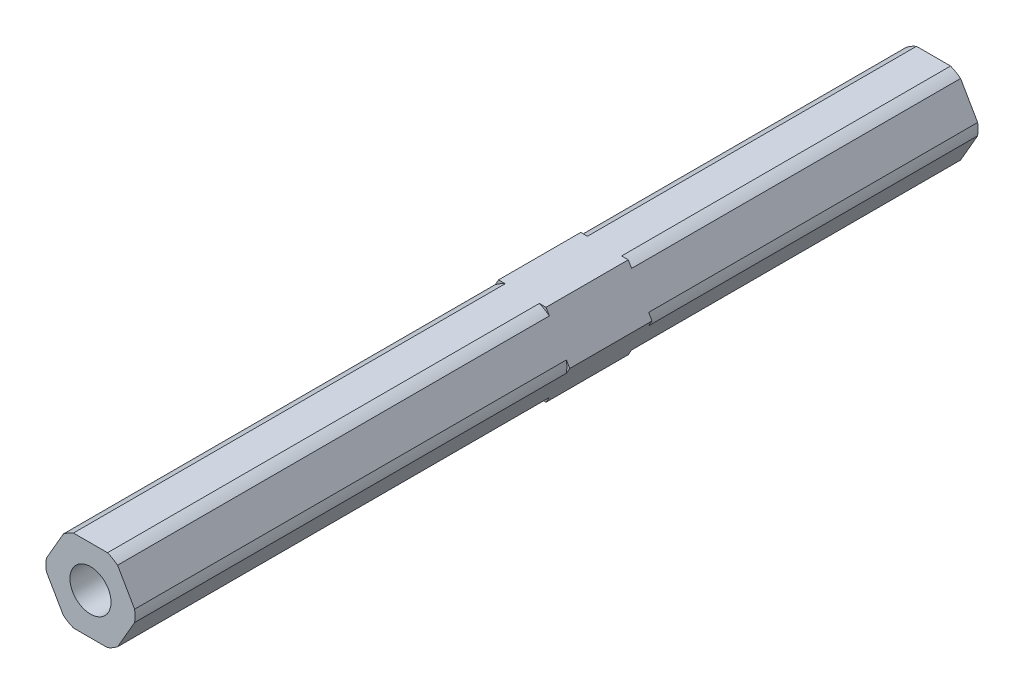
SolidWorks part; units mm, degrees
material "6061-T6 (SS)"
ref_plane "Front Plane" through (0, 0, 0) normal (0, 0, 1) x (1, 0, 0)
ref_plane "Top Plane" through (0, 0, 0) normal (0, 1, 0) x (1, 0, 0)
ref_plane "Right Plane" through (0, 0, 0) normal (1, 0, 0) x (0, 0, -1)
sketch "Sketch1" plane through (0, 0, 0) normal (0, 0, 1) x (1, 0, 0)
  line L1 (3.6662, -6.35) -> (7.3323, 0)
  line L2 (7.3323, 0) -> (3.6662, 6.35)
  line L3 (3.6662, 6.35) -> (-3.6662, 6.35)
  line L4 (-3.6662, 6.35) -> (-7.3323, 0)
  line L5 (-7.3323, 0) -> (-3.6662, -6.35)
  line L6 (-3.6662, -6.35) -> (3.6662, -6.35)
  circle A0 centre (0, 0) radius 6.35 construction
  dimension "D1" = 12.7
extrude "Boss-Extrude1" add sketch "Sketch1" along normal blind 12.7
sketch "Sketch2" plane through (0, 0, 12.7) normal (0, 0, 1) x (1, 0, 0)
  line L0 (-7.3323, 0) -> (-3.6662, -6.35) construction
  line L1 (-3.6662, -6.35) -> (3.6662, -6.35) construction
  line L2 (3.6662, -6.35) -> (7.3323, 0) construction
  line L3 (7.3323, 0) -> (3.6662, 6.35) construction
  line L4 (3.6662, 6.35) -> (-3.6662, 6.35) construction
  line L5 (-3.6662, 6.35) -> (-7.3323, 0) construction
  line L6 (-6.8168, -0.893) -> (-4.1818, -5.457)
  line L7 (-2.635, -6.35) -> (2.635, -6.35)
  line L8 (4.1818, -5.457) -> (6.8168, -0.893)
  line L9 (6.8168, 0.893) -> (4.1818, 5.457)
  line L10 (2.635, 6.35) -> (-2.635, 6.35)
  line L11 (-4.1818, 5.457) -> (-6.8168, 0.893)
  arc A0 (-6.8168, 0.893) -> (-6.8168, -0.893) centre (0, 0) ccw
  arc A1 (-2.635, 6.35) -> (-4.1818, 5.457) centre (0, 0) ccw
  arc A2 (4.1818, 5.457) -> (2.635, 6.35) centre (0, 0) ccw
  arc A3 (6.8168, -0.893) -> (6.8168, 0.893) centre (0, 0) ccw
  arc A4 (2.635, -6.35) -> (4.1818, -5.457) centre (0, 0) ccw
  arc A5 (-4.1818, -5.457) -> (-2.635, -6.35) centre (0, 0) ccw
  dimension "D1" = 13.75
sketch "Sketch3" plane through (0, 0, 0) normal (0, 0, -1) x (-1, 0, 0)
  line L0 (-3.6662, -6.35) -> (-7.3323, 0) construction
  line L1 (3.6662, -6.35) -> (-3.6662, -6.35) construction
  line L2 (7.3323, 0) -> (3.6662, -6.35) construction
  line L3 (3.6662, 6.35) -> (7.3323, 0) construction
  line L4 (-3.6662, 6.35) -> (3.6662, 6.35) construction
  line L5 (-7.3323, 0) -> (-3.6662, 6.35) construction
  line L6 (-4.1818, -5.457) -> (-6.8168, -0.893)
  line L7 (2.635, -6.35) -> (-2.635, -6.35)
  line L8 (6.8168, -0.893) -> (4.1818, -5.457)
  line L9 (4.1818, 5.457) -> (6.8168, 0.893)
  line L10 (-2.635, 6.35) -> (2.635, 6.35)
  line L11 (-6.8168, 0.893) -> (-4.1818, 5.457)
  arc A0 (-6.8168, 0.893) -> (-6.8168, -0.893) centre (0, 0) ccw
  arc A1 (-2.635, 6.35) -> (-4.1818, 5.457) centre (0, 0) ccw
  arc A2 (4.1818, 5.457) -> (2.635, 6.35) centre (0, 0) ccw
  arc A3 (6.8168, -0.893) -> (6.8168, 0.893) centre (0, 0) ccw
  arc A4 (2.635, -6.35) -> (4.1818, -5.457) centre (0, 0) ccw
  arc A5 (-4.1818, -5.457) -> (-2.635, -6.35) centre (0, 0) ccw
  dimension "D1" = 13.75
extrude "Boss-Extrude2" add sketch "Sketch2" along normal blind 66.675
extrude "Boss-Extrude3" add sketch "Sketch3" along normal blind 50.8 contours A1 L11 A0 L6 A5 L7 A4 L8 A3 L9 A2 L10
sketch "Sketch5" plane through (0, 0, 79.375) normal (0, 0, 1) x (1, 0, 0)
  circle A0 centre (0, 0) radius 3.175
  dimension "D1" = 6.35
extrude "Cut-Extrude1" cut sketch "Sketch5" against normal blind 7.62
